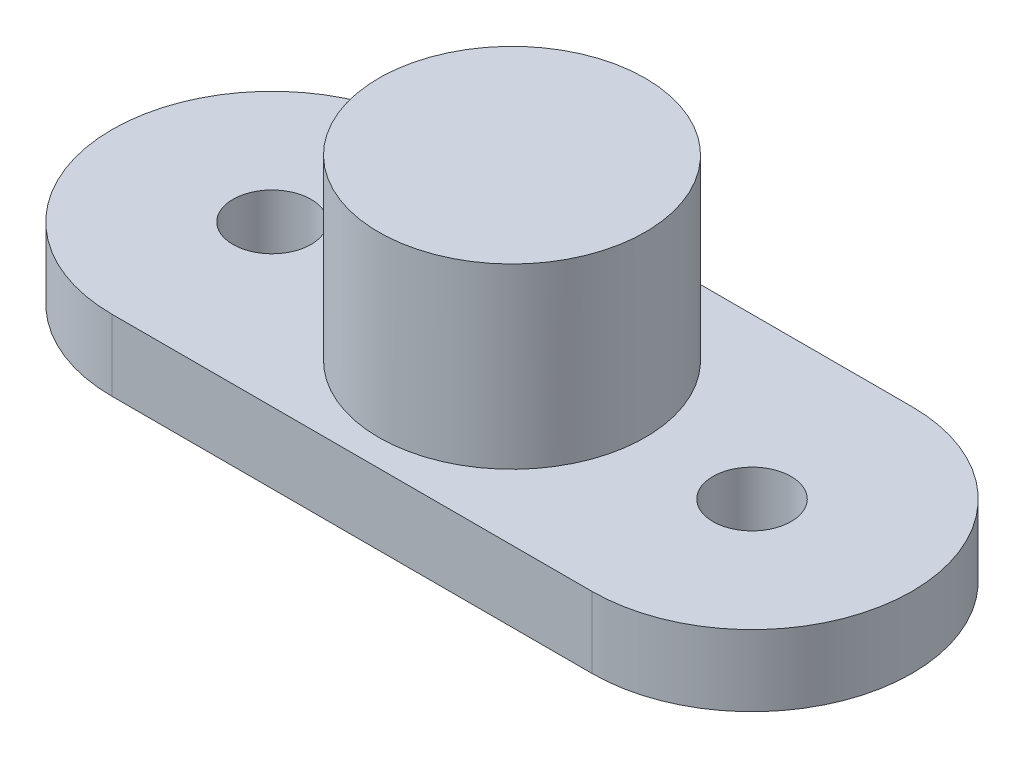
SolidWorks part; units mm, degrees
ref_plane "Front Plane" through (0, 0, 0) normal (0, 0, 1) x (1, 0, 0)
ref_plane "Top Plane" through (0, 0, 0) normal (0, 1, 0) x (1, 0, 0)
ref_plane "Right Plane" through (0, 0, 0) normal (1, 0, 0) x (0, 0, -1)
sketch "Sketch1" plane through (0, 0, 0) normal (0, 1, 0) x (1, 0, 0)
  line L0 (0, 0) -> (6.75, 0)
  line L1 (0, 0) -> (-6.75, 0)
  line L2 (-6.75, 4.4995) -> (6.75, 4.4995)
  line L3 (-6.75, -4.4995) -> (6.75, -4.4995)
  circle A0 centre (-6.75, 0) radius 1.1
  circle A1 centre (6.75, 0) radius 1.1
  arc A2 (6.75, 4.4995) -> (6.75, -4.4995) centre (6.75, 0) cw
  arc A3 (-6.75, 4.4995) -> (-6.75, -4.4995) centre (-6.75, 0) ccw
  circle A6 centre (0, 0) radius 3.75
extrude "Boss-Extrude3" add sketch "Sketch1" along normal blind 2
sketch "Sketch3" plane through (0, 0, 0) normal (0, -1, 0) x (1, 0, 0)
  circle A2 centre (0, 0) radius 3.75
extrude "Boss-Extrude4" add sketch "Sketch3" against normal blind 7
